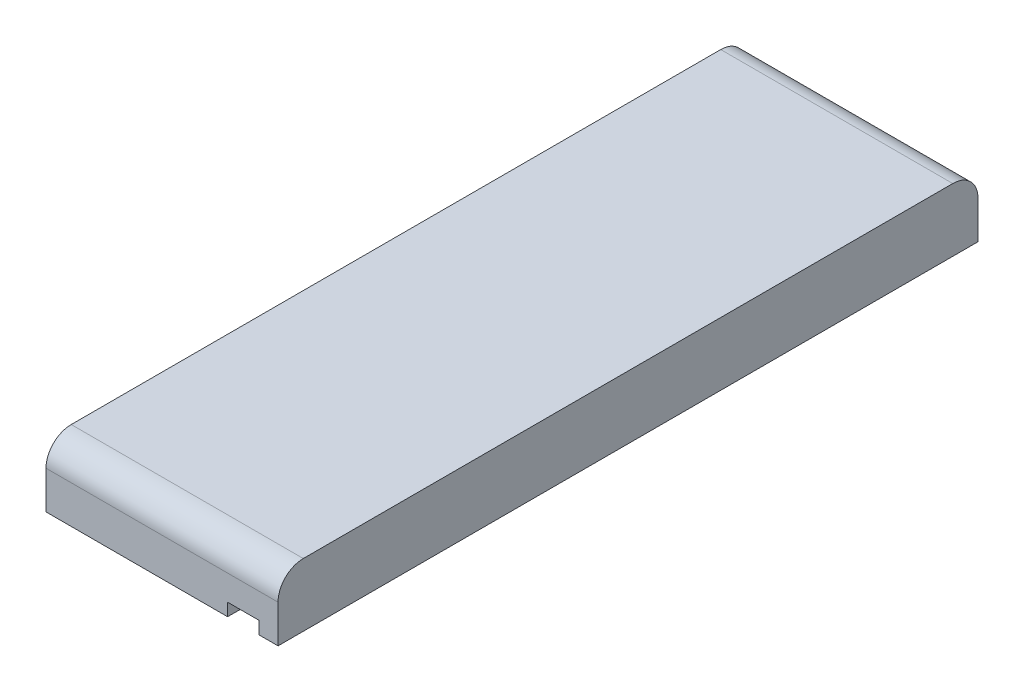
SolidWorks part; units mm, degrees
material "Polyetheretherketone (PEEK)"
ref_plane "Front" through (0, 0, 0) normal (0, 0, 1) x (1, 0, 0)
ref_plane "Top" through (0, 0, 0) normal (0, 1, 0) x (1, 0, 0)
ref_plane "Right" through (0, 0, 0) normal (1, 0, 0) x (0, 0, -1)
sketch "Sketch1" plane through (0, 0, 0) normal (0, 0, 1) x (1, 0, 0)
  line L1 (0, 0) -> (-18.4, 0)
  line L2 (0, 0) -> (0, 5)
  line L3 (0, 5) -> (-18.4, 5)
  line L4 (-18.4, 0) -> (-18.4, 5)
  dimension "D1" = 18.4
  dimension "D2" = 5
extrude "Boss-Extrude1" add sketch "Sketch1" along normal blind 55.5
sketch "Sketch2" plane through (0, 0, 55.5) normal (0, 0, 1) x (1, 0, 0)
  line L0 (-18.4, 0) -> (0, 0) construction
  line L1 (-1.5, 0) -> (-4, 0)
  line L2 (-1.5, 0) -> (-1.5, 1)
  line L3 (-1.5, 1) -> (-4, 1)
  line L4 (-4, 0) -> (-4, 1)
  line L5 (0, 0) -> (0, 5) construction
  dimension "D1" = 1
  dimension "D2" = 2.5
  dimension "D3" = 1.5
extrude "Cut-Extrude1" cut sketch "Sketch2" against normal through all
hole_wizard "M2x0.4 Tapped Hole1" positions "Sketch4" profile "Sketch3" tap size "M2x0.4" standard "ANSI Metric"
sketch "Sketch4" plane through (-18.4, 0, 0) normal (-1, 0, 0) x (0, 0, 1)
  line L0 (55.5, 5) -> (0, 5) construction
  line L1 (0, 5) -> (0, 0) construction
  line L2 (0, 3) -> (3.75, 3) construction
  line L7 (51.75, 3) -> (55.5, 3) construction
  line L8 (55.5, 5) -> (55.5, 0) construction
  line L9 (27.75, 3) -> (27.75, 5) construction
  point P0 (51.75, 3)
  point P4 (27.75, 3)
  point P8 (3.75, 3)
  dimension "D1" = 2
  dimension "D2" = 24
sketch "Sketch3" plane through (-18.4, 3, 51.75) normal (0, 1, 0) x (0, 0, 1)
  line L0 (0, 0) -> (0, 7.4807)
  line L1 (0, 7.4807) -> (0.8, 7)
  line L2 (0.8, 7) -> (0.8, 5)
  line L3 (0.8, 5) -> (1, 5)
  line L4 (1, 5) -> (1, 0)
  line L5 (1, 0) -> (0, 0)
  line L10 (0, 7.4807) -> (-0.8, 7) construction
  line L11 (0, -6.35) -> (0, 107.95) construction
  dimension "Tap Drill Dia." = 1.6
  dimension "Tap Drill Depth" = 7
  dimension "Thread Major Dia." = 2
  dimension "Thread Depth" = 5
  dimension "Drill Angle" = 118
fillet "Fillet1" radius 2 2 edges at (-9.2, 5, 55.5) (-9.2, 5, 0)
hole_wizard "CBORE for M2 SHCS1" positions "Sketch6" profile "Sketch5" counterbore size "M2" standard "ANSI Metric"
sketch "Sketch6" plane through (-19.5, 0, 0) normal (-1, 0, 0) x (0, 0, 1)
  line L0 (47.75, 2.5) -> (7.75, 2.5) construction
  line L1 (7.75, 2.5) -> (27.75, 2.5) construction
  line L2 (27.75, 2.5) -> (27.75, 5) construction
  line L3 (53.5, 5) -> (2, 5) construction
  point P0 (47.75, 2.5)
  point P4 (7.75, 2.5)
  dimension "D1" = 40
  dimension "D2" = 2.5
sketch "Sketch5" plane through (-19.5, 2.5, 47.75) normal (0, 1, 0) x (0, 0, 1)
  line L0 (0, 0) -> (0, 19.5)
  line L1 (0, 19.5) -> (1.2, 19.5)
  line L3 (1.2, 19.5) -> (1.2, 12)
  line L4 (1.2, 12) -> (2.2, 12)
  line L5 (2.2, 12) -> (2.2, 0)
  line L7 (2.2, 0) -> (0, 0)
  line L11 (0, -6.35) -> (0, 107.95) construction
  dimension "Thru Hole Dia." = 2.4
  dimension "Thru Hole Depth" = 19.5
  dimension "C'Bore Dia." = 4.4
  dimension "C'Bore Depth" = 12
